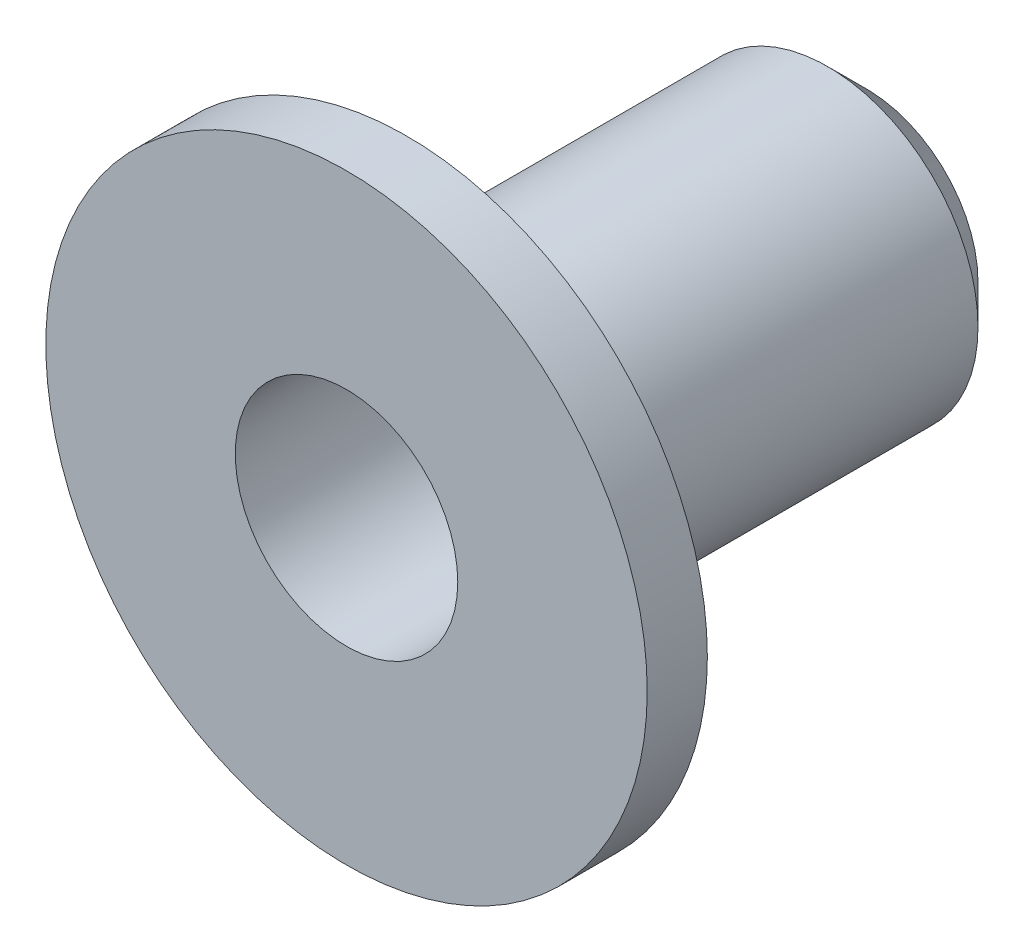
SolidWorks part; units mm, degrees
ref_plane "Plan de face" through (0, 0, 0) normal (0, 0, 1) x (1, 0, 0)
ref_plane "Plan de dessus" through (0, 0, 0) normal (0, 1, 0) x (1, 0, 0)
ref_plane "Plan de droite" through (0, 0, 0) normal (1, 0, 0) x (0, 0, -1)
sketch "Esquisse1" plane through (0, 0, 0) normal (0, 0, 1) x (1, 0, 0)
  circle A1 centre (0, 0) radius 15
  dimension "D1" = 30
extrude "Boss.-Extru.1" add sketch "Esquisse1" along normal blind 3
sketch "Esquisse2" plane through (0, 0, 0) normal (0, 0, -1) x (-1, 0, 0)
  circle A0 centre (0, 0) radius 7.5
  dimension "D1" = 15
extrude "Boss.-Extru.2" add sketch "Esquisse2" along normal blind 23
chamfer "Chanfrein1" distance 2 angle 45 1 edges at (-7.5, 0, -23)
sketch "Esquisse3" plane through (0, 0, -23) normal (0, 0, -1) x (-1, 0, 0)
  circle A0 centre (0, 0) radius 5.55
  dimension "D1" = 11.1
extrude "Enlèv. mat.-Extru.1" cut sketch "Esquisse3" against normal blind 23
sketch "Esquisse4" plane through (0, 0, 3) normal (0, 0, 1) x (1, 0, 0)
  circle A0 centre (0, 0) radius 5.55
  dimension "D1" = 11.1
extrude "Enlèv. mat.-Extru.2" cut sketch "Esquisse4" against normal blind 26
